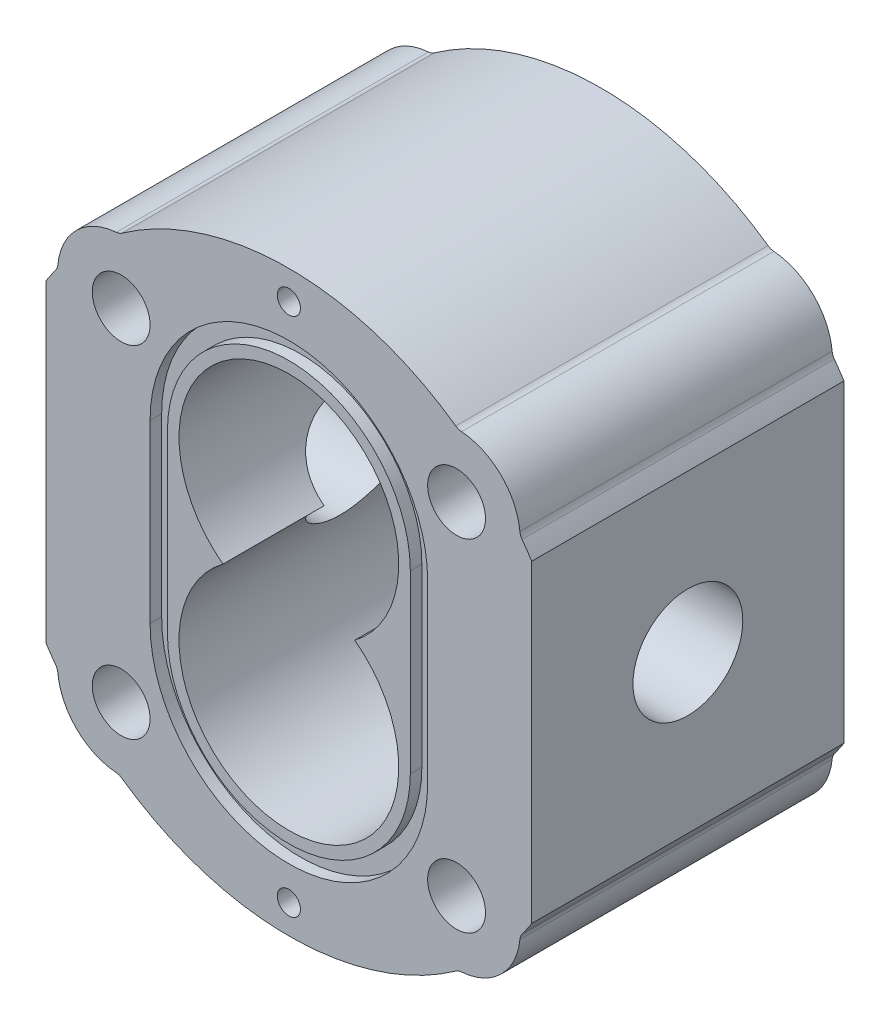
SolidWorks part; units mm, degrees
ref_plane "Front Plane" through (0, 0, 0) normal (0, 0, 1) x (1, 0, 0)
ref_plane "Top Plane" through (0, 0, 0) normal (0, 1, 0) x (1, 0, 0)
ref_plane "Right Plane" through (0, 0, 0) normal (1, 0, 0) x (0, 0, -1)
sketch "Sketch2" plane through (0, 0, 0) normal (0, 0, 1) x (1, 0, 0)
  line L0 (-60.9931, -15.2) -> (60.9931, -15.2) construction
  line L1 (0, 52.8602) -> (0, -83.2602) construction
  line L2 (54.187, -65.2) -> (-54.187, -65.2) construction
  line L3 (42, 11.9293) -> (42, -42.3293)
  line L4 (42, -65.2) -> (42, -111.0363)
  line L5 (-42, 11.9293) -> (-42, -42.3293)
  arc A0 (11.4, -15.2) -> (-11.4, -15.2) centre (0, 0) ccw
  arc A1 (-11.4, -15.2) -> (11.4, -15.2) centre (0, -30.4) ccw
  arc A2 (28.8646, 25.6269) -> (-28.8646, 25.6269) centre (0, -15.2) ccw
  circle A4 centre (29, -44.7) radius 5
  circle A5 centre (29, 14.3) radius 5
  circle A6 centre (-29, 14.3) radius 5
  circle A7 centre (-29, -44.7) radius 5
  arc A8 (39.9498, 15.3497) -> (29.8624, 25.2661) centre (29, 14.3) ccw
  arc A9 (-39.9498, 15.3497) -> (-29.8624, 25.2661) centre (-29, 14.3) cw
  arc A10 (-39.9498, -45.7497) -> (-29.8624, -55.6661) centre (-29, -44.7) ccw
  arc A11 (39.9498, -45.7497) -> (29.8624, -55.6661) centre (29, -44.7) cw
  arc A12 (-40.3276, 14.3582) -> (-42, 11.9293) centre (0, -15.2) ccw
  arc A13 (-28.8646, -56.0269) -> (28.8646, -56.0269) centre (0, -15.2) ccw
  arc A14 (40.3276, -44.7582) -> (42, -42.3293) centre (0, -15.2) ccw
  arc A15 (42, 11.9293) -> (40.3276, 14.3582) centre (0, -15.2) ccw
  arc A16 (-42, -42.3293) -> (-40.3276, -44.7582) centre (0, -15.2) ccw
  arc A17 (-39.9498, -45.7497) -> (-40.3276, -44.7582) centre (-41.9407, -45.9405) ccw
  arc A18 (-29.8624, -55.6661) -> (-28.8646, -56.0269) centre (-30.0191, -57.66) cw
  arc A19 (29.8624, -55.6661) -> (28.8646, -56.0269) centre (30.0191, -57.66) ccw
  arc A20 (39.9498, -45.7497) -> (40.3276, -44.7582) centre (41.9407, -45.9405) cw
  arc A21 (39.9498, 15.3497) -> (40.3276, 14.3582) centre (41.9407, 15.5405) ccw
  arc A22 (29.8624, 25.2661) -> (28.8646, 25.6269) centre (30.0191, 27.26) cw
  arc A23 (-29.8624, 25.2661) -> (-28.8646, 25.6269) centre (-30.0191, 27.26) ccw
  arc A24 (-39.9498, 15.3497) -> (-40.3276, 14.3582) centre (-41.9407, 15.5405) cw
  point P8 (0, -15.2)
  point P16 (0, -15.2)
  point P31 (0, -65.2)
  point P39 (-39.9879, -45.2161)
  point P42 (-29.3283, -55.6951)
  point P45 (29.3283, -55.6951)
  point P48 (39.9879, -45.2161)
  point P51 (39.9879, 14.8161)
  point P54 (29.3283, 25.2951)
  point P57 (-29.3283, 25.2951)
  point P60 (-39.9879, 14.8161)
  dimension "D1" = 38
  dimension "D2" = 38
  dimension "D3" = 100
  dimension "D7" = 10
  dimension "D8" = 22
  dimension "D11" = 2
  dimension "D4" = 15.2
  dimension "D5" = 29.5
  dimension "D6" = 29
  dimension "D9" = 108.3739
  dimension "D10" = 42
extrude "Boss-Extrude1" add sketch "Sketch2" along normal mid plane 54 contours A9 A24 A12 L5 A16 A17 A10 A18 A13 A19 A11 A20 A14 L3 A15 A21 A8 A22 A2 A23 A7 A6 A1 A0 A4 A5
sketch "Sketch3" plane through (42, 0, 0) normal (1, 0, 0) x (0, 0, -1)
  circle A0 centre (0, -15.2) radius 9.5
  dimension "D1" = 19
extrude "Cut-Extrude2" cut sketch "Sketch3" against normal through all contours A0
sketch "Sketch5" plane through (0, 0, -27) normal (0, 0, -1) x (-1, 0, 0)
  line L0 (-24, 0) -> (-24, -30.4)
  line L1 (24, -30.4) -> (24, 0)
  line L2 (-21, 0) -> (-21, -30.4)
  line L3 (21, -30.4) -> (21, 0)
  arc A0 (24, 0) -> (-24, 0) centre (0, 0) ccw
  arc A1 (-24, -30.4) -> (24, -30.4) centre (0, -30.4) ccw
  arc A2 (-21, -30.4) -> (21, -30.4) centre (0, -30.4) ccw
  arc A3 (21, 0) -> (-21, 0) centre (0, 0) ccw
  dimension "D1" = 48
  dimension "D2" = 48
  dimension "D3" = 21
  dimension "3" = 3
extrude "Cut-Extrude3" cut sketch "Sketch5" against normal blind 2
sketch "Sketch6" plane through (0, 0, -27) normal (0, 0, -1) x (-1, 0, 0)
  circle A0 centre (0, 29.8) radius 2
  circle A1 centre (0, -60.2) radius 2
  dimension "D1" = 4
extrude "Cut-Extrude4" cut sketch "Sketch6" against normal blind 3
mirror "Mirror1" about plane through (0, 0, 0) normal (0, 0, 1) of "Cut-Extrude3", "Cut-Extrude4"
sketch "Sketch7" plane through (42, 0, 0) normal (1, 0, 0) x (0, 0, -1)
  circle A1 centre (0, -15.2) radius 9.5
